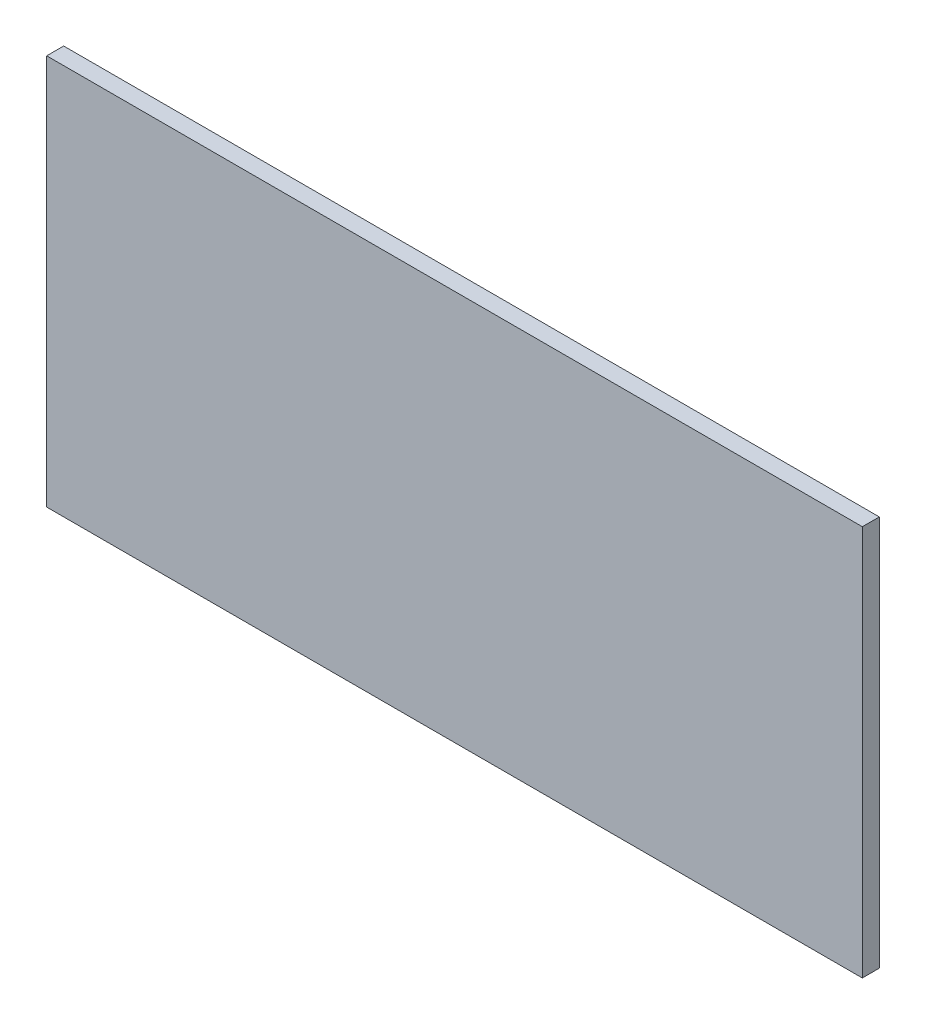
SolidWorks part; units mm, degrees
ref_plane "Front Plane" through (0, 0, 0) normal (0, 0, 1) x (1, 0, 0)
ref_plane "Top Plane" through (0, 0, 0) normal (0, 1, 0) x (1, 0, 0)
ref_plane "Right Plane" through (0, 0, 0) normal (1, 0, 0) x (0, 0, -1)
sketch "Sketch1" plane through (0, 0, 0) normal (0, 0, 1) x (1, 0, 0)
  line L1 (0, 0) -> (609.6, 0)
  line L2 (0, 0) -> (0, 292.1)
  line L3 (0, 292.1) -> (609.6, 292.1)
  line L4 (609.6, 0) -> (609.6, 292.1)
  dimension "D1" = 292.1
  dimension "D2" = 609.6
extrude "Boss-Extrude1" add sketch "Sketch1" along normal blind 12.7
